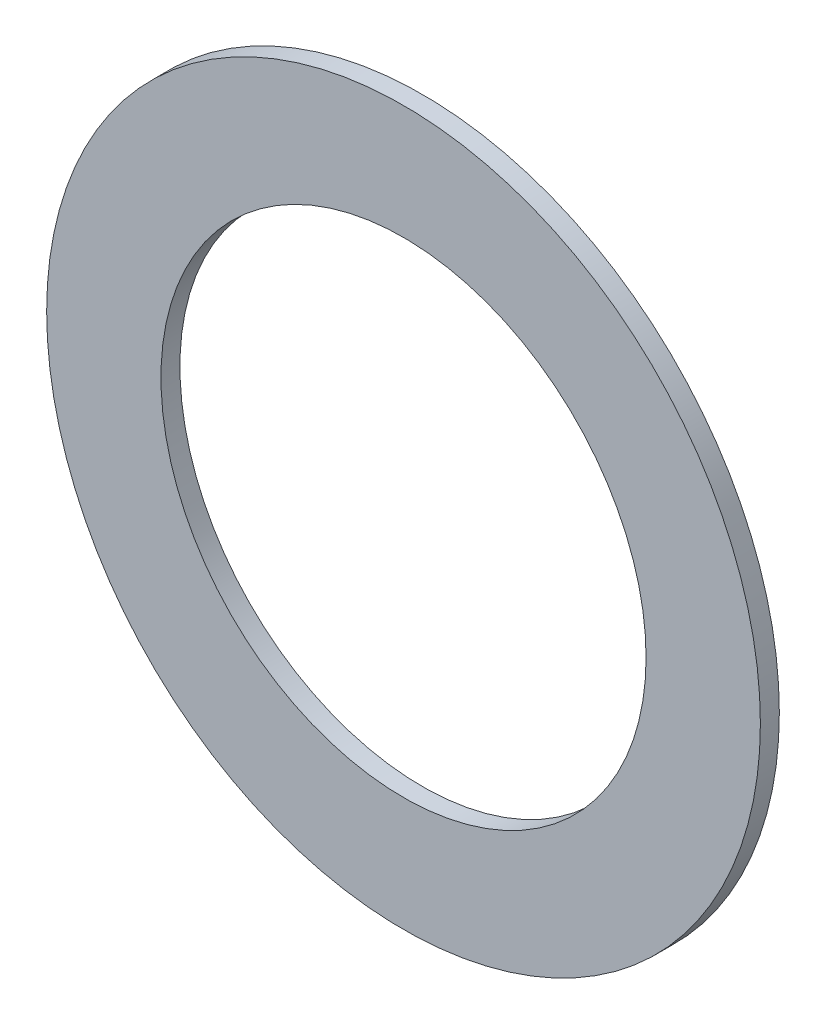
SolidWorks part; units mm, degrees
material "Barium"
ref_plane "Front" through (0, 0, 0) normal (0, 0, 1) x (1, 0, 0)
ref_plane "Top" through (0, 0, 0) normal (0, 1, 0) x (1, 0, 0)
ref_plane "Right" through (0, 0, 0) normal (1, 0, 0) x (0, 0, -1)
sketch "Sketch1" plane through (0, 0, 0) normal (0, 0, 1) x (1, 0, 0)
  circle A0 centre (0, 0) radius 128
  circle A1 centre (0, 0) radius 87
extrude "Boss-Extrude2" add sketch "Sketch1" along normal blind 6.8 separate body contours A0 | A1
